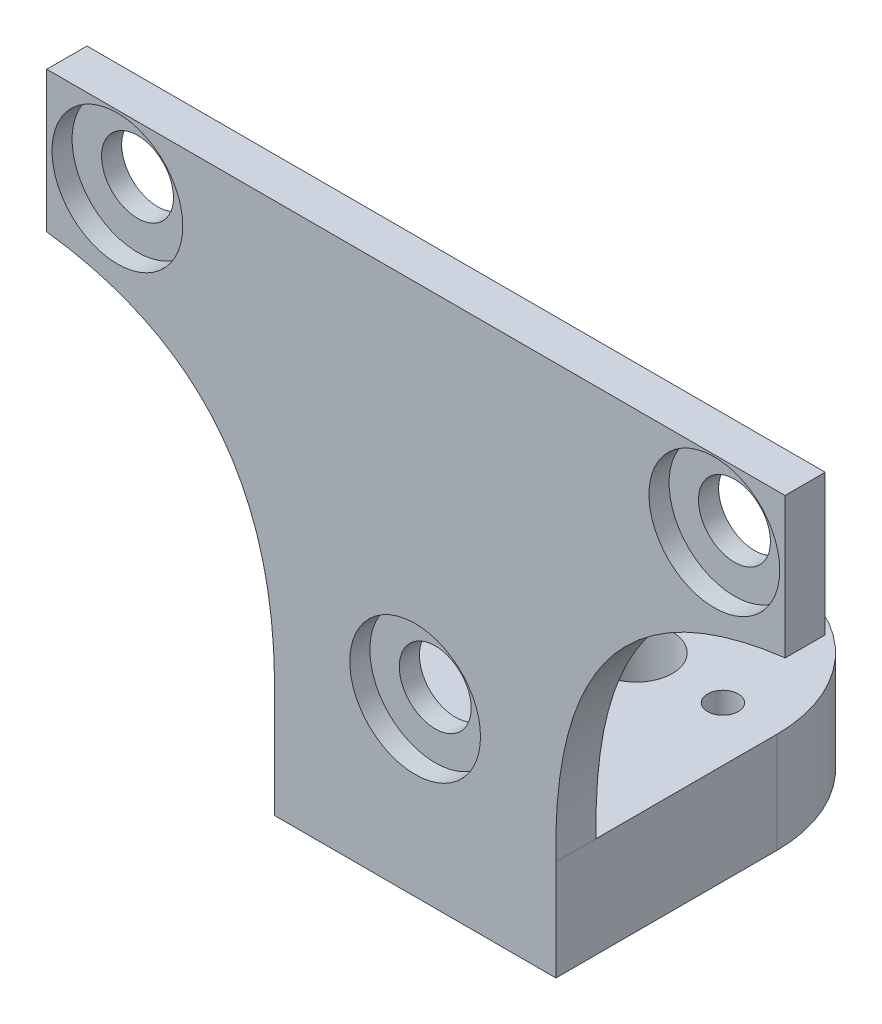
SolidWorks part; units mm, degrees
ref_plane "Plan de face" through (0, 0, 0) normal (0, 0, 1) x (1, 0, 0)
ref_plane "Plan de dessus" through (0, 0, 0) normal (0, 1, 0) x (1, 0, 0)
ref_plane "Plan de droite" through (0, 0, 0) normal (1, 0, 0) x (0, 0, -1)
sketch "Esquisse1" plane through (0, 0, 0) normal (0, 0, 1) x (1, 0, 0)
  line L0 (0, 42.9324) -> (0, 28.9324)
  line L1 (73.4, 42.9324) -> (73.4, 28.9324)
  line L2 (36.625, 0) -> (22.625, 0)
  line L3 (36.625, 0) -> (50.625, 0)
  line L4 (73.25, 28.9324) -> (73.4, 28.9324)
  line L19 (0, 42.9324) -> (73.4, 42.9324)
  circle A0 centre (7.025, 36.1785) radius 3.575
  circle A1 centre (66.375, 36.2459) radius 3.575
  circle A2 centre (36.625, 7.025) radius 3.575
  spline S0 degree 2 poles (0, 28.9324) (23.2174, 26.0221) (22.625, 0) knots 0 0 0 1 1 1
  spline S1 degree 2 poles (73.25, 28.9324) (50.0326, 26.0221) (50.625, 0) knots 0 0 0 1 1 1
extrude "Boss.-Extru.1" add sketch "Esquisse1" along normal blind 4
sketch "Esquisse17" plane through (0, 0, 4) normal (0, 0, 1) x (1, 0, 0)
  circle A0 centre (7.025, 36.1785) radius 6.5
  circle A1 centre (66.375, 36.2459) radius 6.5
  circle A2 centre (36.625, 7.025) radius 6.5
  dimension "D1" = 13
  dimension "D2" = 13
  dimension "D3" = 13
extrude "Enlèv. mat.-Extru.9" cut sketch "Esquisse17" against normal blind 2
sketch "Esquisse18" plane through (0, 0, 0) normal (0, -1, 0) x (1, 0, 0)
  line L0 (22.625, -18) -> (22.625, 4)
  line L1 (50.625, -18) -> (50.625, 4)
  line L2 (22.625, 4) -> (50.625, 4)
  arc A0 (22.625, -18) -> (50.625, -18) centre (36.625, -18) ccw
  circle A1 centre (36.625, -18) radius 3.575
  circle A2 centre (28.025, -18) radius 1.525
  circle A3 centre (45.225, -18) radius 1.525
extrude "Boss.-Extru.6" add sketch "Esquisse18" along normal blind 10
sketch "Esquisse22" plane through (0, 0, 0) normal (0, 1, 0) x (1, 0, 0)
  line L2 (22.625, 0) -> (50.6299, 0)
  line L3 (22.625, 0) -> (22.625, 39.8017)
  line L4 (22.625, 39.8017) -> (50.6299, 39.8017)
  line L5 (50.6299, 0) -> (50.6299, 39.8017)
